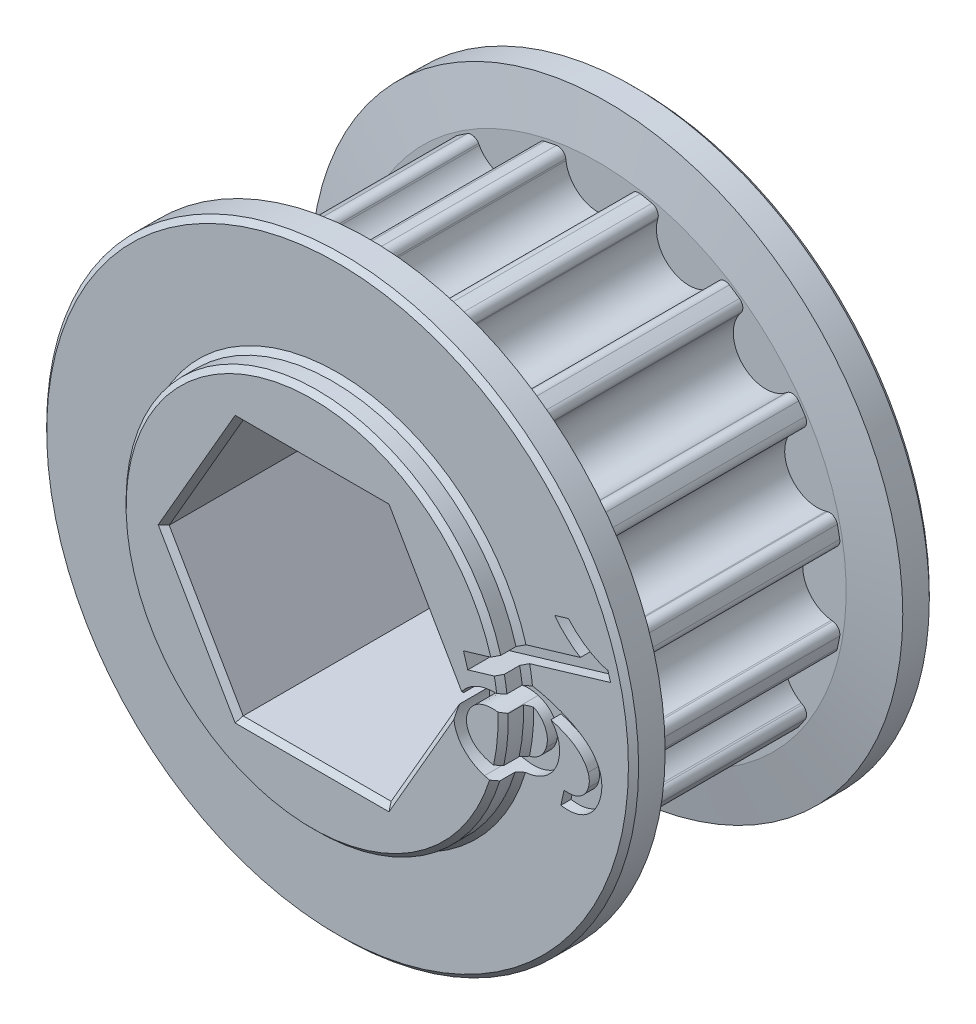
SolidWorks part; units mm, degrees
material "ABS"
ref_plane "Front Plane" through (0, 0, 0) normal (0, 0, 1) x (1, 0, 0)
ref_plane "Top Plane" through (0, 0, 0) normal (0, 1, 0) x (1, 0, 0)
ref_plane "Right Plane" through (0, 0, 0) normal (1, 0, 0) x (0, 0, -1)
sketch "Sketch2" plane through (0, 0, 0) normal (0, 0, 1) x (1, 0, 0)
  circle A0 centre (0, 0) radius 12.2146
extrude "pulley" add sketch "Sketch2" along normal mid plane 11
sketch "tooth" plane through (0, 0, 0) normal (0, 0, 1) x (1, 0, 0)
  line L0 (0, 0) -> (0, 11.8146) construction
  line L1 (4.8868, 10.7566) -> (0, 11.8146) construction
  line L2 (4.8868, 10.7566) -> (0, 0) construction
  line L3 (-2.1327, 15.8502) -> (-1.6129, 11.6165)
  line L6 (2.1327, 15.8502) -> (1.6129, 11.6165)
  line L7 (-2.1327, 15.8502) -> (2.1327, 15.8502)
  arc A1 (-1.6129, 11.6165) -> (1.6129, 11.6165) centre (0, 11.8146) ccw
  arc A2 (0, 11.8146) -> (4.8868, 10.7566) centre (0, 0) cw construction
  circle A3 centre (4.8868, 10.7566) radius 1.625 construction
extrude "cut tooth" cut sketch "tooth" against normal mid plane 11
fillet "blend tooth" radius 0.4 2 edges at (1.6722, 12.0996, 0) (-1.6722, 12.0996, 0)
pattern_circular "tooth pattern" count 16 over 360 about axis through (0, 0, 0) along (0, 0, 1) of "cut tooth", "blend tooth"
sketch "Sketch3" plane through (0, 0, 0) normal (0, 0, 1) x (1, 0, 0)
  circle A0 centre (0, 0) radius 14.7546
  circle A1 centre (0, 0) radius 12.2146 construction
  dimension "D1" = 2.54
extrude "sidewall" add sketch "Sketch3" along normal blind 2 from offset 5.5
mirror "mirror sidewall" about plane through (0, 0, 0) normal (0, 0, 1) of "sidewall"
chamfer "sidewall chamfer" distance 2.4 angle 10 2 edges at (14.7546, 0, 5.5) (14.7546, 0, -5.5)
sketch "Sketch5" plane through (0, 0, 0) normal (0, 0, 1) x (1, 0, 0)
  circle A0 centre (0, 0) radius 9.525
  dimension "D1" = 19.05
extrude "bearing spacer (Manual Suppress)" add sketch "Sketch5" along normal blind 8.77 and the other way blind 8.77
sketch "Sketch4" plane through (0, 0, 0) normal (0, 0, 1) x (1, 0, 0)
  line L1 (3.6882, 6.3881) -> (-3.6882, 6.3881)
  line L2 (-3.6882, 6.3881) -> (-7.3763, 0)
  line L3 (-7.3763, 0) -> (-3.6882, -6.3881)
  line L4 (-3.6882, -6.3881) -> (3.6882, -6.3881)
  line L5 (3.6882, -6.3881) -> (7.3763, 0)
  line L6 (7.3763, 0) -> (3.6882, 6.3881)
  circle A0 centre (0, 0) radius 6.3881 construction
  dimension "D1" = 12.7762
extrude "hex shaft" cut sketch "Sketch4" against normal mid plane 127
chamfer "chamfers" distance 0.254 angle 45 18 edges at (14.7546, 0, -7.5) (14.7546, 0, 7.5) (-9.525, 0, -7.5) (9.525, 0, 7.5) (9.525, 0, 8.77) (0, 6.3881, 8.77) (-5.5323, 3.194, 8.77) (-5.5323, -3.194, 8.77) (0, -6.3881, 8.77) (5.5323, -3.194, 8.77) (5.5323, 3.1941, 8.77) (9.525, 0, -8.77) (0, -6.3881, -8.77) (-5.5323, -3.194, -8.77) (-5.5323, 3.194, -8.77) (0, 6.3881, -8.77) (5.5323, 3.1941, -8.77) (5.5323, -3.194, -8.77)
sketch "SK-VersaCut" plane through (0, 0, 0) normal (0, 0, 1) x (1, 0, 0)
  line B0 (6.3387, 23.6565) -> (5.299, 19.7762)
  line B1 (14.4772, 14.4772) -> (17.3177, 17.3177)
  line B2 (23.6565, 6.3387) -> (19.7762, 5.299)
  line B3 (19.7762, -5.299) -> (23.6565, -6.3387)
  line B4 (17.3177, -17.3177) -> (14.4772, -14.4772)
  line B5 (5.299, -19.7762) -> (6.3387, -23.6565)
  line B6 (-6.3387, -23.6565) -> (-5.299, -19.7762)
  line B7 (-14.4772, -14.4772) -> (-17.3177, -17.3177)
  line B8 (-23.6565, -6.3387) -> (-19.7762, -5.299)
  line B9 (-19.7762, 5.299) -> (-23.6565, 6.3387)
  line B10 (-17.3177, 17.3177) -> (-14.4772, 14.4772)
  line B11 (-5.299, 19.7762) -> (-6.3387, 23.6565)
  circle B12 centre (0, 23.8125) radius 2.2479
  arc B13 (5.9535, 18.5765) -> (13.1109, 14.4442) centre (0, 0) cw
  arc B14 (7.5904, 24.3458) -> (17.2889, 18.7464) centre (0, 0) cw
  arc B15 (5.9535, 18.5765) -> (5.299, 19.7762) centre (6.2559, 19.5198) cw
  arc B16 (13.1109, 14.4442) -> (14.4772, 14.4772) centre (13.7767, 15.1777) ccw
  arc B17 (17.2889, 18.7464) -> (17.3177, 17.3177) centre (16.6173, 18.0182) cw
  arc B18 (7.5904, 24.3458) -> (6.3387, 23.6565) centre (7.2956, 23.4001) ccw
  circle B19 centre (20.6222, 11.9062) radius 2.2479
  arc B20 (19.0645, 4.1323) -> (19.0645, -4.1323) centre (0, 0) cw
  arc B21 (24.8793, 5.5994) -> (24.8793, -5.5994) centre (0, 0) cw
  arc B22 (19.0645, 4.1323) -> (19.7762, 5.299) centre (20.0326, 4.3422) cw
  arc B23 (19.0645, -4.1323) -> (19.7762, -5.299) centre (20.0326, -4.3422) ccw
  arc B24 (24.8793, -5.5994) -> (23.6565, -6.3387) centre (23.9129, -5.3819) cw
  arc B25 (24.8793, 5.5994) -> (23.6565, 6.3387) centre (23.9129, 5.3819) ccw
  circle B26 centre (20.6222, -11.9063) radius 2.2479
  arc B27 (13.1109, -14.4442) -> (5.9535, -18.5765) centre (0, 0) cw
  arc B28 (17.2889, -18.7464) -> (7.5904, -24.3458) centre (0, 0) cw
  arc B29 (13.1109, -14.4442) -> (14.4772, -14.4772) centre (13.7767, -15.1777) cw
  arc B30 (5.9535, -18.5765) -> (5.299, -19.7762) centre (6.2559, -19.5198) ccw
  arc B31 (7.5904, -24.3458) -> (6.3387, -23.6565) centre (7.2956, -23.4001) cw
  arc B32 (17.2889, -18.7464) -> (17.3177, -17.3177) centre (16.6173, -18.0182) ccw
  circle B33 centre (0, -23.8125) radius 2.2479
  arc B34 (-5.9535, -18.5765) -> (-13.1109, -14.4442) centre (0, 0) cw
  arc B35 (-7.5904, -24.3458) -> (-17.2889, -18.7464) centre (0, 0) cw
  arc B36 (-5.9535, -18.5765) -> (-5.299, -19.7762) centre (-6.2559, -19.5198) cw
  arc B37 (-13.1109, -14.4442) -> (-14.4772, -14.4772) centre (-13.7767, -15.1777) ccw
  arc B38 (-17.2889, -18.7464) -> (-17.3177, -17.3177) centre (-16.6173, -18.0182) cw
  arc B39 (-7.5904, -24.3458) -> (-6.3387, -23.6565) centre (-7.2956, -23.4001) ccw
  circle B40 centre (-20.6222, -11.9063) radius 2.2479
  arc B41 (-19.0645, -4.1323) -> (-19.0645, 4.1323) centre (0, 0) cw
  arc B42 (-24.8793, -5.5994) -> (-24.8793, 5.5994) centre (0, 0) cw
  arc B43 (-19.0645, -4.1323) -> (-19.7762, -5.299) centre (-20.0326, -4.3422) cw
  arc B44 (-19.0645, 4.1323) -> (-19.7762, 5.299) centre (-20.0326, 4.3422) ccw
  arc B45 (-24.8793, 5.5994) -> (-23.6565, 6.3387) centre (-23.9129, 5.3819) cw
  arc B46 (-24.8793, -5.5994) -> (-23.6565, -6.3387) centre (-23.9129, -5.3819) ccw
  circle B47 centre (-20.6222, 11.9063) radius 2.2479
  arc B48 (-13.1109, 14.4442) -> (-5.9535, 18.5765) centre (0, 0) cw
  arc B49 (-17.2889, 18.7464) -> (-7.5904, 24.3458) centre (0, 0) cw
  arc B50 (-13.1109, 14.4442) -> (-14.4772, 14.4772) centre (-13.7767, 15.1777) cw
  arc B51 (-5.9535, 18.5765) -> (-5.299, 19.7762) centre (-6.2559, 19.5198) ccw
  arc B52 (-7.5904, 24.3458) -> (-6.3387, 23.6565) centre (-7.2956, 23.4001) cw
  arc B53 (-17.2889, 18.7464) -> (-17.3177, 17.3177) centre (-16.6173, 18.0182) ccw
sketch_block_instance "VersaKey-1"
sketch_block "Block1" parameters "D1"=47.625, "D2"=4.4958, "D3"=19.5072, "D4"=25.5016, "D6"=0.9906, "D5"=30
extrude "VersaKey (Manual Suppress)" [suppressed] cut sketch "SK-VersaCut" against normal through all both and the other way through all
sketch "Lightening Holes" plane through (0, 0, 0) normal (0, 0, 1) x (1, 0, 0)
  line L0 (-0.4116, 5.7929) -> (-3.9521, 11.9253)
  line L1 (3.9521, 11.9253) -> (0.4116, 5.7929)
  line L14 (0, 0) -> (-3.6662, 6.35) construction
  line L15 (0, 0) -> (0, 6.35) construction
  line L24 (0, 0) -> (3.6662, 6.35) construction
  line L25 (0, 6.35) -> (-3.6662, 6.35) construction
  line L26 (0, 6.35) -> (3.6662, 6.35) construction
  line L27 (-3.0943, 11.43) -> (3.0943, 11.43)
  line L28 (0, 6.35) -> (0, 11.43) construction
  line L29 (4.811, 3.2529) -> (8.3515, 9.3853)
  line L30 (8.3515, 8.3947) -> (11.4458, 3.0353)
  line L31 (12.3037, 2.54) -> (5.2225, 2.54)
  line L32 (5.2225, -2.54) -> (12.3037, -2.54)
  line L33 (11.4458, -3.0353) -> (8.3515, -8.3947)
  line L34 (8.3515, -9.3853) -> (4.811, -3.2529)
  line L35 (0.4116, -5.7929) -> (3.9521, -11.9253)
  line L36 (3.0943, -11.43) -> (-3.0943, -11.43)
  line L37 (-3.9521, -11.9253) -> (-0.4116, -5.7929)
  line L38 (-4.811, -3.2529) -> (-8.3515, -9.3853)
  line L39 (-8.3515, -8.3947) -> (-11.4458, -3.0353)
  line L40 (-12.3037, -2.54) -> (-5.2225, -2.54)
  line L41 (-5.2225, 2.54) -> (-12.3037, 2.54)
  line L42 (-11.4458, 3.0353) -> (-8.3515, 8.3947)
  line L43 (-8.3515, 9.3853) -> (-4.811, 3.2529)
  arc A3 (0.5164, 7.2763) -> (-0.5164, 7.2763) centre (0, 0) cw
  arc A4 (-3.0943, 11.43) -> (-3.9521, 11.9253) centre (-3.0943, 12.4206) cw
  arc A5 (3.0943, 11.43) -> (3.9521, 11.9253) centre (3.0943, 12.4206) ccw
  arc A6 (-0.5164, 7.2763) -> (0.4116, 5.7929) centre (-0.4463, 6.2882) cw
  arc A7 (0.5164, 7.2763) -> (-0.4116, 5.7929) centre (0.4463, 6.2882) ccw
  arc A72 (6.5597, 3.1909) -> (6.0432, 4.0854) centre (0, 0) cw
  arc A73 (6.5597, 3.1909) -> (4.811, 3.2529) centre (5.6689, 2.7576) ccw
  arc A74 (8.3515, 8.3947) -> (8.3515, 9.3853) centre (9.2094, 8.89) cw
  arc A75 (6.0432, 4.0854) -> (5.2225, 2.54) centre (5.2225, 3.5306) cw
  arc A76 (6.0432, -4.0854) -> (6.5597, -3.1909) centre (0, 0) cw
  arc A77 (6.0432, -4.0854) -> (5.2225, -2.54) centre (5.2225, -3.5306) ccw
  arc A78 (11.4458, -3.0353) -> (12.3037, -2.54) centre (12.3037, -3.5306) cw
  arc A79 (6.5597, -3.1909) -> (4.811, -3.2529) centre (5.6689, -2.7576) cw
  arc A80 (-0.5164, -7.2763) -> (0.5164, -7.2763) centre (0, 0) cw
  arc A81 (-0.5164, -7.2763) -> (0.4116, -5.7929) centre (-0.4463, -6.2882) ccw
  arc A82 (3.0943, -11.43) -> (3.9521, -11.9253) centre (3.0943, -12.4206) cw
  arc A83 (0.5164, -7.2763) -> (-0.4116, -5.7929) centre (0.4463, -6.2882) cw
  arc A84 (-6.5597, -3.1909) -> (-6.0432, -4.0854) centre (0, 0) cw
  arc A85 (-6.5597, -3.1909) -> (-4.811, -3.2529) centre (-5.6689, -2.7576) ccw
  arc A86 (-8.3515, -8.3947) -> (-8.3515, -9.3853) centre (-9.2094, -8.89) cw
  arc A87 (-6.0432, -4.0854) -> (-5.2225, -2.54) centre (-5.2225, -3.5306) cw
  arc A88 (-6.0432, 4.0854) -> (-6.5597, 3.1909) centre (0, 0) cw
  arc A89 (-6.0432, 4.0854) -> (-5.2225, 2.54) centre (-5.2225, 3.5306) ccw
  arc A90 (-11.4458, 3.0353) -> (-12.3037, 2.54) centre (-12.3037, 3.5306) cw
  arc A91 (-6.5597, 3.1909) -> (-4.811, 3.2529) centre (-5.6689, 2.7576) cw
  arc A92 (11.4458, 3.0353) -> (12.3037, 2.54) centre (12.3037, 3.5306) ccw
  arc A93 (8.3515, -8.3947) -> (8.3515, -9.3853) centre (9.2094, -8.89) ccw
  arc A94 (-3.0943, -11.43) -> (-3.9521, -11.9253) centre (-3.0943, -12.4206) ccw
  arc A95 (-11.4458, -3.0353) -> (-12.3037, -2.54) centre (-12.3037, -3.5306) ccw
  arc A96 (-8.3515, 8.3947) -> (-8.3515, 9.3853) centre (-9.2094, 8.89) ccw
  point P72 (0, 0)
  point P77 (0, 0)
  point P87 (0, 0)
extrude "Lightening Holes (Man Suppress)" [suppressed] cut sketch "Lightening Holes" against normal through all both and the other way through all
sketch "Sketch6" plane through (0, 0, 0) normal (0, 0, 1) x (1, 0, 0)
  line L0 (0, 8.1927) -> (0, 0) construction
  line L1 (0, 0) -> (0, -8.1927) construction
  arc A1 (0, 8.1927) -> (0, -8.1927) centre (0, 0) cw construction
  arc A2 (0, 8.1927) -> (0, -8.1927) centre (0, 0) ccw construction
  text T0 "16\r\n" font "DS-Digital" height in points 24
extrude "4419" cut sketch "Sketch6" along normal blind 2.54 from offset 6.992
equation "\"INPUT_pulley_teeth\"= 16"
equation "\"pulley_c2c\"= 5mm"
equation "\"pulley_teeth_deg\"= 360 / \"INPUT_pulley_teeth\""
equation "\"pulley_radius\"= ( \"pulley_c2c\" / ( 2 * cos ( \"iso_half_angle\" ) ) ) - 1mm"
equation "\"iso_half_angle\"= ( 180 - \"pulley_teeth_deg\" ) / 2"
equation "\"D1@tooth\" = \"pulley_radius\""
equation "\"pulley_tooth_dia\"= 3.25mm"
equation "\"D3@tooth\"=\"pulley_c2c\""
equation "\"D2@tooth\"=\"pulley_tooth_dia\""
equation "\"D1@Sketch2\"=2* \"pulley_radius\"+\"pulley_tooth_offset\""
equation "\"pulley_tooth_offset\"= .8mm"
equation "\"D1@tooth pattern\" = \"INPUT_pulley_teeth\""
equation "\"INPUT_pulley_belt_9_or_15_(unitless)\"= 9"
equation "\"D1@pulley\"=\"pulley_width\""
equation "\"D19@sidewall\" =  ( \"pulley_width\" / 2 ) "
equation "\"D1@sidewall\"=\"pulley_sidewall_thick\""
equation "\"pulley_width\"= IIF ( \"INPUT_pulley_belt_9_or_15_(unitless)\" = 9 , 11mm , 17mm )"
equation "\"D1@cut tooth\"=\"pulley_width\""
equation "\"D1@sidewall chamfer\" = 2.4mm"
equation "\"D4@Lightening Holes\"=\"pulley_radius\"-\"pulley_tooth_dia\"-.05"
equation "\"D1@bearing spacer (Manual Suppress)\" = 0.05 +  ( \"pulley_width\" / 2 )  + \"pulley_sidewall_thick\""
equation "\"D2@bearing spacer (Manual Suppress)\" = 0.05 +  ( \"pulley_width\" / 2 )  + \"pulley_sidewall_thick\""
equation "\"pulley_sidewall_thick\"= 2mm"
equation "\"D1@4419\" = \"pulley_width\""
equation "\"D19@4419\"=(\"pulley_width\" / 2) +\"pulley_sidewall_thick\" - 0.02"
equation "\"rad_len\" = \"INPUT_pulley_teeth\" * \"pulley_c2c\""
